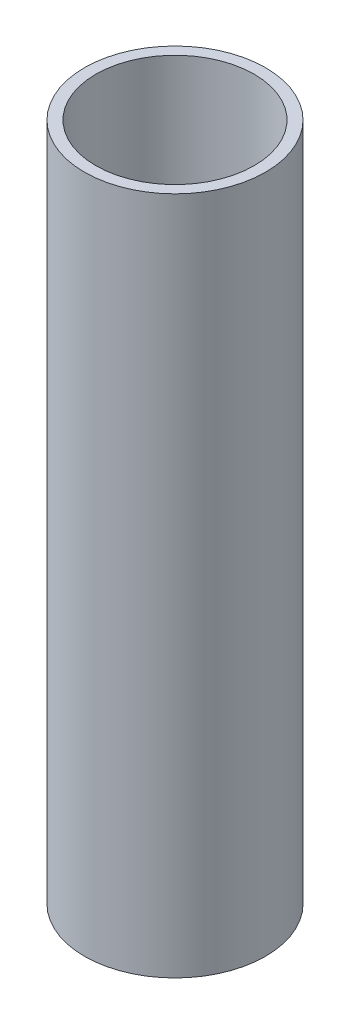
SolidWorks part; units mm, degrees
material "Hexcel AS4C (3000 丝)"
ref_plane "前视基准面" through (0, 0, 0) normal (0, 0, 1) x (1, 0, 0)
ref_plane "上视基准面" through (0, 0, 0) normal (0, 1, 0) x (1, 0, 0)
ref_plane "右视基准面" through (0, 0, 0) normal (1, 0, 0) x (0, 0, -1)
other "Configuration Table"
sketch "草图1" plane through (0, 0, 0) normal (0, 1, 0) x (1, 0, 0)
  circle A0 centre (0, 0) radius 8
  circle A1 centre (0, 0) radius 7
  dimension "D1" = 16
  dimension "D2" = 1
extrude "凸台-拉伸1" add sketch "草图1" along normal blind 60
